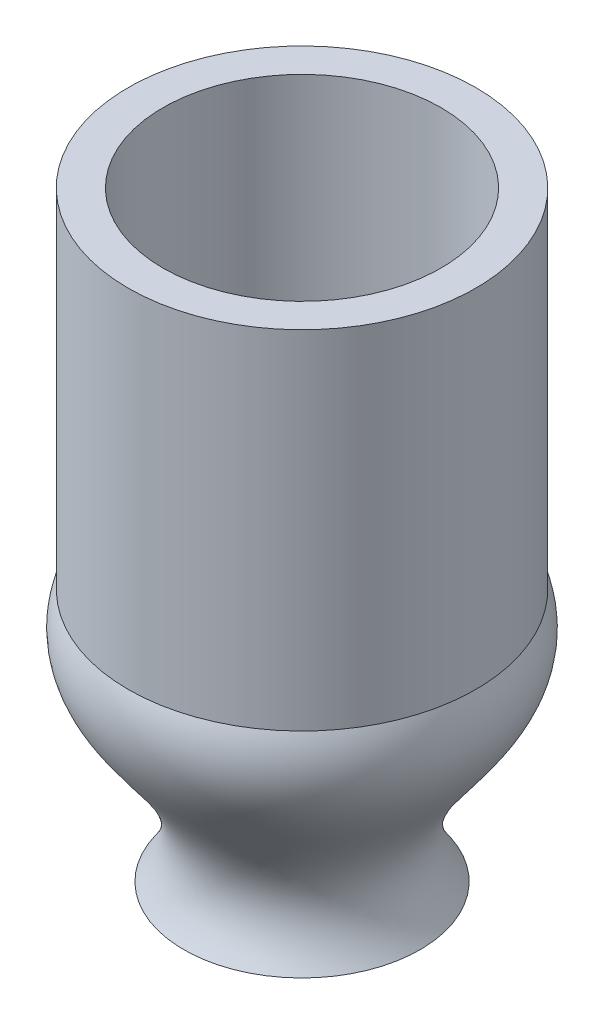
SolidWorks part; units mm, degrees
ref_plane "Спереди" through (0, 0, 0) normal (0, 0, 1) x (1, 0, 0)
ref_plane "Сверху" through (0, 0, 0) normal (0, 1, 0) x (1, 0, 0)
ref_plane "Справа" through (0, 0, 0) normal (1, 0, 0) x (0, 0, -1)
other "Configuration Table"
sketch "Эскиз9" plane through (0, 0, 0) normal (0, 0, 1) x (1, 0, 0)
  line L0 (32.7639, 30.1621) -> (32.7639, 80.1621)
  line L1 (32.7639, 80.1621) -> (27.7639, 80.1621)
  line L2 (19.7639, -6.2601) -> (24.7639, -6.2601)
  line L3 (27.7639, 80.1621) -> (27.7639, 30.1621)
  line L4 (-20.4364, -6.2601) -> (19.7639, -6.2601) construction
  line L5 (7.7639, -6.2601) -> (7.7639, 55.7983) construction
  spline S0 degree 3 poles (24.7639, -6.2601) (14.0957, 8.0323) (38.85, 14.9603) (32.7639, 30.1621) knots 0 0 0 0 1 1 1 1
  spline S1 degree 3 poles (27.7639, 30.1621) (31.8006, 15.4488) (9.4717, 8.3609) (19.7639, -6.2601) knots 0 0 0 0 1 1 1 1
  dimension "D6" = 50
  dimension "D1" = 5
  dimension "D2" = 5
  dimension "D3" = 5
  dimension "D4" = 5
  dimension "D5" = 5
  dimension "D7" = 17
  dimension "D8" = 25
revolve "Повернуть1" add sketch "Эскиз9" angle 360 about L5
